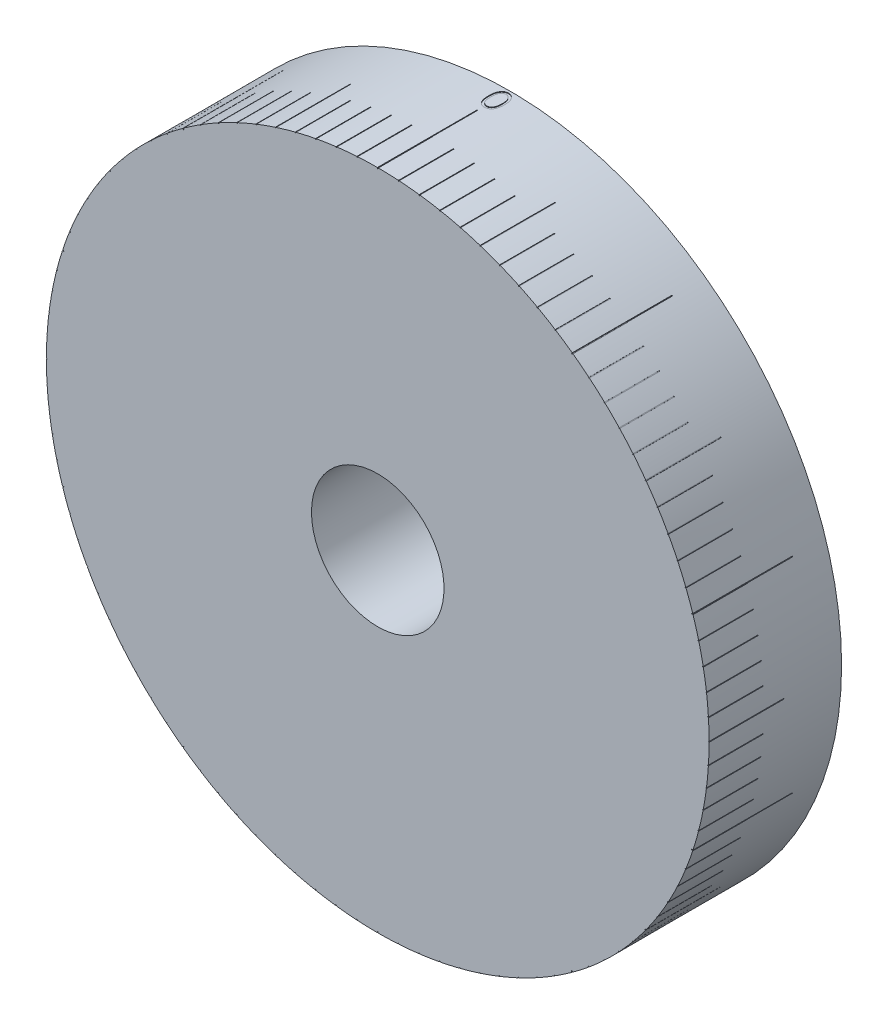
SolidWorks part; units mm, degrees
ref_plane "Přední rovina" through (0, 0, 0) normal (0, 0, 1) x (1, 0, 0)
ref_plane "Horní rovina" through (0, 0, 0) normal (0, 1, 0) x (1, 0, 0)
ref_plane "Pravá rovina" through (0, 0, 0) normal (1, 0, 0) x (0, 0, -1)
sketch "Skica1" plane through (0, 0, 0) normal (1, 0, 0) x (0, 0, -1)
  line L1 (0, 0) -> (20, 0)
  line L2 (0, 0) -> (0, 50)
  line L3 (0, 50) -> (20, 50)
  line L4 (20, 0) -> (20, 50)
  dimension "D1" = 50
  dimension "D2" = 20
revolve "Rotovat1" add sketch "Skica1" angle 360 about L1
ref_plane "Rovina1" through (0, 50, 0) normal (0, 1, 0) x (1, 0, 0)
sketch "Skica5" plane through (0, 50, 0) normal (0, 1, 0) x (1, 0, 0)
  line L0 (0, 0) -> (0, 15) construction
  line L1 (0, 20) -> (0, 0) construction
  line L2 (-0.05, 0) -> (-0.05, 15)
  line L3 (0.05, 0) -> (0.05, 15)
  arc A0 (-0.05, 0) -> (0.05, 0) centre (0, 0) ccw
  arc A1 (0.05, 15) -> (-0.05, 15) centre (0, 15) ccw
  point P5 (0, 7.5)
extrude "Odebrat vysunutím1" cut sketch "Skica5" against normal blind 0.2
pattern_circular "Kruhové pole17" count 10 every 36 about axis through (0, 0, 0) along (0, 0, 1) of "Odebrat vysunutím1"
sketch "Skica7" plane through (0, 0, -20) normal (0, 0, -1) x (-1, 0, 0)
  circle A0 centre (0, 0) radius 44.8863
  circle A1 centre (0, 0) radius 20.4467
extrude "Odebrat vysunutím2" cut sketch "Skica7" against normal blind 15
sketch "Skica8" plane through (0, 0, -5) normal (0, 0, -1) x (-1, 0, 0)
  circle A0 centre (0, 0) radius 10
  dimension "D1" = 20
extrude "Odebrat vysunutím3" cut sketch "Skica8" along normal through all and the other way blind 15
sketch "Skica10" plane through (0, 0, 0) normal (0, 0, 1) x (1, 0, 0)
  line L0 (0, 0) -> (0, 53.7349) construction
  circle A0 centre (0, 0) radius 50
  point P4 (0, 50)
  point P8 (3.1395, 49.9013)
  point P9 (6.2667, 49.6057)
  point P10 (9.3691, 49.1144)
  point P11 (12.4345, 48.4292)
  point P12 (15.4508, 47.5528)
  point P13 (18.4062, 46.4888)
  point P14 (21.289, 45.2414)
  point P15 (24.0877, 43.8153)
  point P16 (26.7913, 42.2164)
  point P17 (29.3893, 40.4508)
  point P18 (31.8712, 38.5257)
  point P19 (34.2274, 36.4484)
  point P20 (36.4484, 34.2274)
  point P21 (38.5257, 31.8712)
  point P22 (40.4508, 29.3893)
  point P23 (42.2164, 26.7913)
  point P24 (43.8153, 24.0877)
  point P25 (45.2414, 21.289)
  point P26 (46.4888, 18.4062)
  point P27 (47.5528, 15.4508)
  point P28 (48.4292, 12.4345)
  point P29 (49.1144, 9.3691)
  point P30 (49.6057, 6.2667)
  point P31 (49.9013, 3.1395)
  point P32 (50, 0)
  point P33 (49.9013, -3.1395)
  point P34 (49.6057, -6.2667)
  point P35 (49.1144, -9.3691)
  point P36 (48.4292, -12.4345)
  point P37 (47.5528, -15.4508)
  point P38 (46.4888, -18.4062)
  point P39 (45.2414, -21.289)
  point P40 (43.8153, -24.0877)
  point P41 (42.2164, -26.7913)
  point P42 (40.4508, -29.3893)
  point P43 (38.5257, -31.8712)
  point P44 (36.4484, -34.2274)
  point P45 (34.2274, -36.4484)
  point P46 (31.8712, -38.5257)
  point P47 (29.3893, -40.4508)
  point P48 (26.7913, -42.2164)
  point P49 (24.0877, -43.8153)
  point P50 (21.289, -45.2414)
  point P51 (18.4062, -46.4888)
  point P52 (15.4508, -47.5528)
  point P53 (12.4345, -48.4292)
  point P54 (9.3691, -49.1144)
  point P55 (6.2667, -49.6057)
  point P56 (3.1395, -49.9013)
  point P57 (0, -50)
  point P58 (-3.1395, -49.9013)
  point P59 (-6.2667, -49.6057)
  point P60 (-9.3691, -49.1144)
  point P61 (-12.4345, -48.4292)
  point P62 (-15.4508, -47.5528)
  point P63 (-18.4062, -46.4888)
  point P64 (-21.289, -45.2414)
  point P65 (-24.0877, -43.8153)
  point P66 (-26.7913, -42.2164)
  point P67 (-29.3893, -40.4508)
  point P68 (-31.8712, -38.5257)
  point P69 (-34.2274, -36.4484)
  point P70 (-36.4484, -34.2274)
  point P71 (-38.5257, -31.8712)
  point P72 (-40.4508, -29.3893)
  point P73 (-42.2164, -26.7913)
  point P74 (-43.8153, -24.0877)
  point P75 (-45.2414, -21.289)
  point P76 (-46.4888, -18.4062)
  point P77 (-47.5528, -15.4508)
  point P78 (-48.4292, -12.4345)
  point P79 (-49.1144, -9.3691)
  point P80 (-49.6057, -6.2667)
  point P81 (-49.9013, -3.1395)
  point P82 (-50, 0)
  point P83 (-49.9013, 3.1395)
  point P84 (-49.6057, 6.2667)
  point P85 (-49.1144, 9.3691)
  point P86 (-48.4292, 12.4345)
  point P87 (-47.5528, 15.4508)
  point P88 (-46.4888, 18.4062)
  point P89 (-45.2414, 21.289)
  point P90 (-43.8153, 24.0877)
  point P91 (-42.2164, 26.7913)
  point P92 (-40.4508, 29.3893)
  point P93 (-38.5257, 31.8712)
  point P94 (-36.4484, 34.2274)
  point P95 (-34.2274, 36.4484)
  point P96 (-31.8712, 38.5257)
  point P97 (-29.3893, 40.4508)
  point P98 (-26.7913, 42.2164)
  point P99 (-24.0877, 43.8153)
  point P100 (-21.289, 45.2414)
  point P101 (-18.4062, 46.4888)
  point P102 (-15.4508, 47.5528)
  point P103 (-12.4345, 48.4292)
  point P104 (-9.3691, 49.1144)
  point P105 (-6.2667, 49.6057)
  point P106 (-3.1395, 49.9013)
  point P107 (0, 0)
  dimension "D1" = 100
ref_plane "Rovina2" through (-15.4508, 47.5528, 0) normal (0.309, -0.9511, 0) x (0, 0, 1)
sketch "Skica12" plane through (-15.4508, 47.5528, 0) normal (0.309, -0.9511, 0) x (0, 0, 1)
  line L1 (-11.2988, -0.1) -> (0, -0.1)
  line L2 (-11.2988, -0.1) -> (-11.2988, 0)
  line L3 (-11.2988, 0) -> (0, 0)
  line L4 (0, -0.1) -> (0, 0)
  dimension "D1" = 0.1
extrude "Odebrat vysunutím4" cut sketch "Skica12" along normal blind 0.1
pattern_circular "Kruhové pole19" count 10 over 360 about axis through (0, 0, 0) along (0, 0, 1) of "Odebrat vysunutím4"
ref_plane "Rovina3" through (-18.3251, 46.5209, 0) normal (-0.3665, 0.9304, 0) x (0, 0, 1)
sketch "Skica13" plane through (-18.3251, 46.5209, 0) normal (-0.3665, 0.9304, 0) x (0, 0, 1)
  line L1 (0, 0) -> (-8.2679, 0)
  line L2 (0, 0) -> (0, -0.1)
  line L3 (0, -0.1) -> (-8.2679, -0.1)
  line L4 (-8.2679, 0) -> (-8.2679, -0.1)
  dimension "D1" = 0.1
extrude "Odebrat vysunutím5" cut sketch "Skica13" against normal blind 0.1
pattern_circular "Kruhové pole21" count 100 every 3.6 about axis through (0, 0, 0) along (0, 0, 1) of "Odebrat vysunutím5"
sketch "Skica15" plane through (0, 50, 0) normal (0, 1, 0) x (1, 0, 0)
  text T0 "0"
extrude "Odebrat vysunutím7" cut sketch "Skica15" against normal blind 0.1
